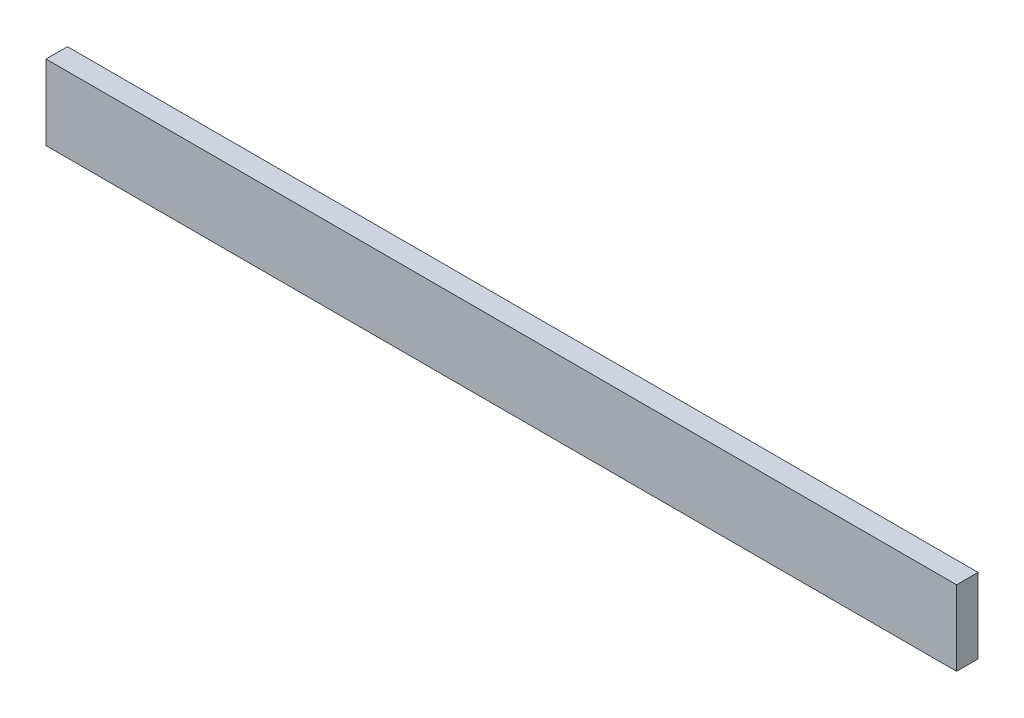
SolidWorks part; units mm, degrees
ref_plane "Front Plane" through (0, 0, 0) normal (0, 0, 1) x (1, 0, 0)
ref_plane "Top Plane" through (0, 0, 0) normal (0, 1, 0) x (1, 0, 0)
ref_plane "Right Plane" through (0, 0, 0) normal (1, 0, 0) x (0, 0, -1)
sketch "Sketch1" plane through (0, 0, 0) normal (0, 0, 1) x (1, 0, 0)
  line L1 (0, 0) -> (85, 0)
  line L2 (0, 0) -> (0, 7)
  line L3 (0, 7) -> (85, 7)
  line L4 (85, 0) -> (85, 7)
  dimension "D1" = 7
  dimension "D2" = 85
extrude "Boss-Extrude1" add sketch "Sketch1" along normal blind 2
